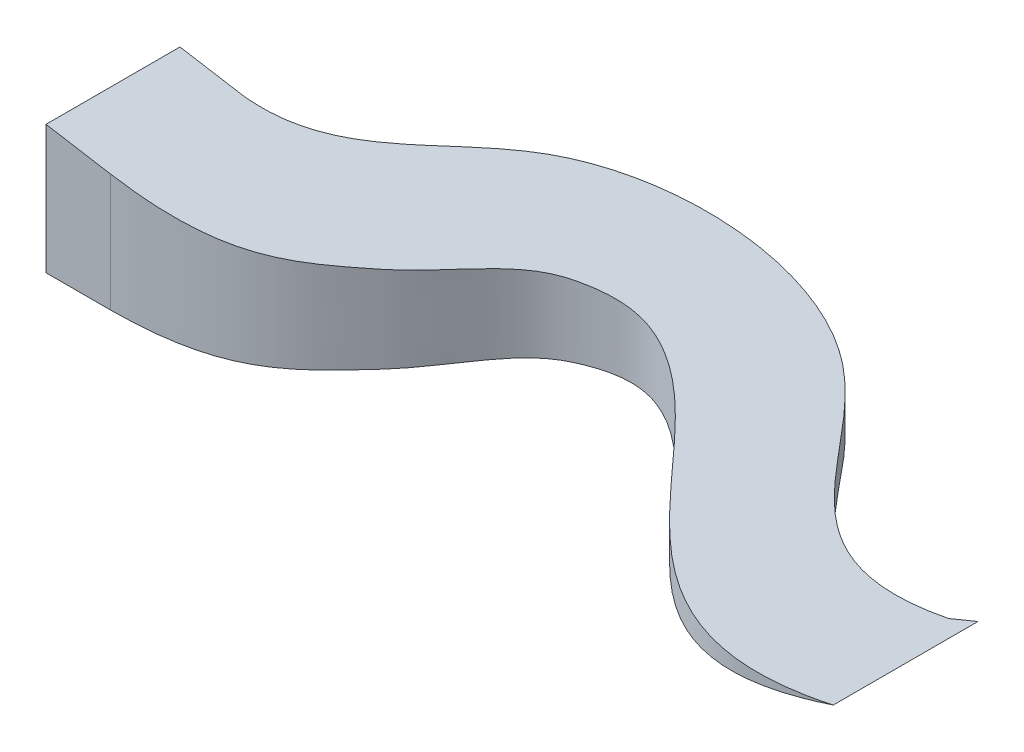
SolidWorks part; units mm, degrees
ref_plane "Front Plane" through (0, 0, 0) normal (0, 0, 1) x (1, 0, 0)
ref_plane "Top Plane" through (0, 0, 0) normal (0, 1, 0) x (1, 0, 0)
ref_plane "Right Plane" through (0, 0, 0) normal (1, 0, 0) x (0, 0, -1)
sketch "Sketch2" plane through (0, 0, 0) normal (0, 1, 0) x (1, 0, 0)
  line L0 (-196.7813, -5) -> (103.2187, -5)
  line L1 (-196.7813, -5) -> (-196.7813, 620) construction
  line L3 (-196.7813, -5) -> (103.2187, -5) construction
  line L5 (2222.8186, 1284.7943) -> (2804.5881, 695.5099)
  line L6 (3386.2389, 760.2462) -> (3386.2389, 85.0661)
  line L10 (3386.2389, 85.0661) -> (3386.2389, 760.2462) construction
  line L11 (988.3751, 402.5548) -> (1372.2317, 851.1327)
  line L12 (2430.1317, 276.9455) -> (1790.5499, 874.4906)
  line L13 (-196.7813, -5) -> (-196.7813, 595)
  line L16 (103.2187, 620) -> (-196.7813, 620)
  line L17 (-196.7813, 620) -> (-196.7813, 595)
  line L18 (920.3448, 1239.1858) -> (495.9912, 789.4197)
  line L19 (2195.0192, 1312.9528) -> (2198.7778, 1309.1456)
  line L20 (3386.2389, 760.2462) -> (3317.0354, 692.0282)
  arc A0 (103.2187, 620) -> (495.9912, 789.4197) centre (103.2187, 1160) ccw
  arc A1 (103.2187, -5) -> (988.3751, 402.5548) centre (103.2187, 1160) ccw
  arc A2 (1790.5499, 874.4906) -> (1372.2317, 851.1327) centre (1592.571, 662.5841) ccw
  arc A4 (2804.5881, 695.5099) -> (3317.0354, 692.0282) centre (3062.5539, 950.1859) ccw
  arc A6 (2431.9635, 275.2341) -> (3386.2389, 85.0661) centre (3062.5539, 950.1859) ccw
  arc A7 (2222.8186, 1284.7943) -> (920.3448, 1239.1858) centre (1592.571, 662.5841) ccw
  point P1 (0, 0)
  point P4 (0, 0)
  dimension "D8" = 2330
  dimension "D9" = 1080
  dimension "D10" = 580
  dimension "D13" = 725
sketch3d "3DSketch1"
  line L0 (3386.2389, 0, -760.2462) -> (3386.2389, 611.9185, -760.2462)
  line L2 (-196.7813, 0, 5) -> (-196.7813, 39.2023, 5)
ref_plane "Plane1" through (0, 0, 0) normal (0, 1, 0) x (1, 0, 0)
sketch "Sketch3" plane through (0, 0, 0) normal (0, 1, 0) x (1, 0, 0)
  line L0 (103.2187, 620) -> (-196.7813, 620)
  line L1 (-196.7813, 620) -> (-196.7813, -5)
  line L2 (-196.7813, -5) -> (103.2187, -5)
  line L3 (3386.2389, 85.0661) -> (3386.2389, 760.2462)
  spline S0 degree 3 poles (103.2187, -5) (588.1952, -3.1639) (771.9646, 163.7992) (1094.0727, 516.9613) (1231.5566, 783.163) (1553.4618, 941.6944) (2236.259, 839.9545) (2563.0648, -321.1586) (3386.2389, 85.0661) knots 0 0 0 0 0.16919 0.199378 0.290494 0.314772 0.430766 1 1 1 1
  spline S1 degree 1 poles (3386.2389, 760.2462) (3317.0354, 692.0282) knots 0 0 1 1
  spline S2 degree 3 poles (3317.0354, 692.0282) (2719.2854, 421.3433) (2458.9586, 1613.401) (791.3452, 1472.7107) (517.504, 642.6496) (103.2187, 620) knots 0 0 0 0 0.371434 0.71736 1 1 1 1
extrude "Boss-Extrude1" add sketch "Sketch3" along normal blind 600
sketch "Sketch4" plane through (0, 0, 0) normal (0, 0, 1) x (1, 0, 0)
  line L0 (-196.7813, 600) -> (3386.2389, 0)
  line L1 (3386.2389, 0) -> (3386.2389, 600)
  line L2 (3386.2389, 600) -> (-196.7813, 600)
  line L3 (-196.7813, 600) -> (-210.3203, 601.2974)
extrude "Cut-Extrude1" cut sketch "Sketch4" against normal blind 1980 and the other way blind 1980 contours L0 L1 L2
